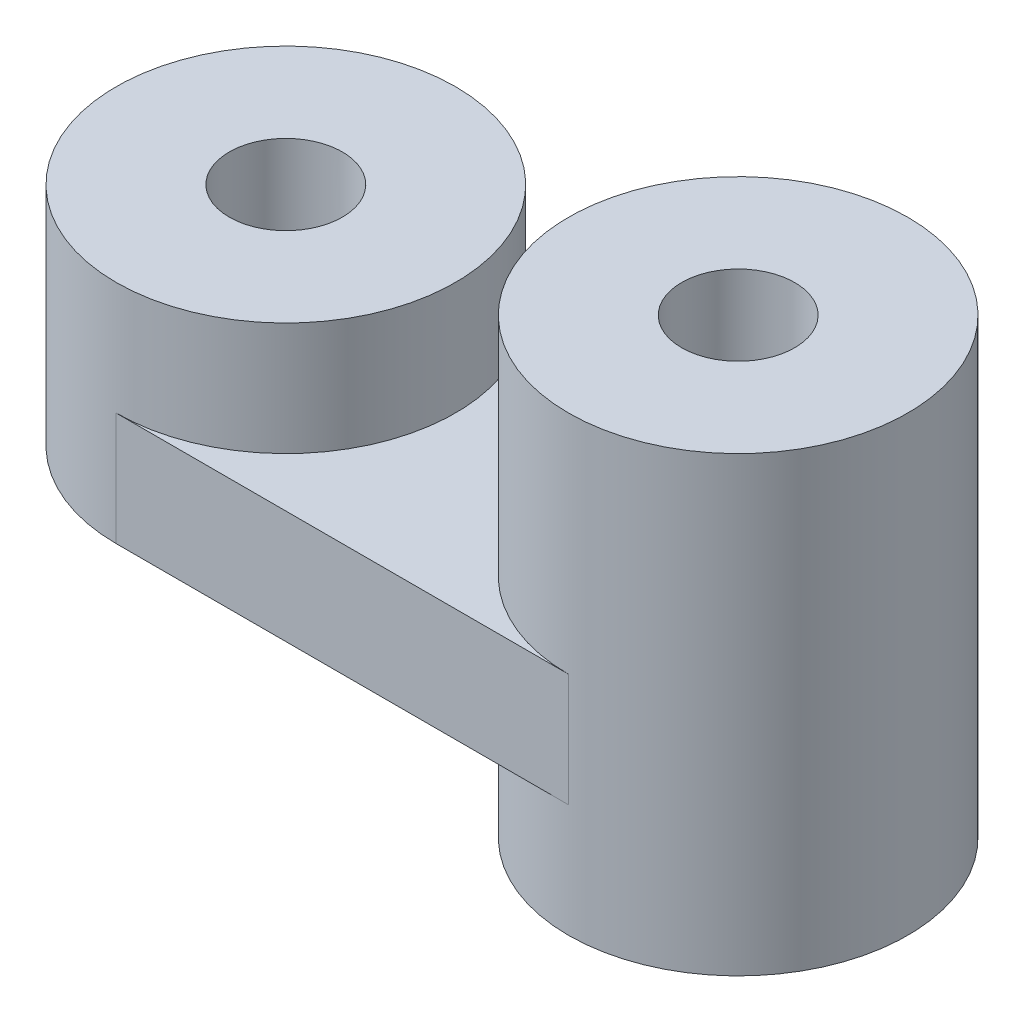
SolidWorks part; units mm, degrees
ref_plane "Alzado" through (0, 0, 0) normal (0, 0, 1) x (1, 0, 0)
ref_plane "Planta" through (0, 0, 0) normal (0, 1, 0) x (1, 0, 0)
ref_plane "Vista lateral" through (0, 0, 0) normal (1, 0, 0) x (0, 0, -1)
sketch "Croquis1" plane through (0, 0, 0) normal (0, 1, 0) x (1, 0, 0)
  line L0 (0, 0) -> (-5, 0) construction
  line L5 (0, 0) -> (15, 0)
  line L6 (0, 0) -> (0, -15)
  line L7 (0, -15) -> (15, -15)
  line L8 (15, 0) -> (15, -15)
  line L9 (0, 0) -> (-20, 0)
  line L10 (0, 0) -> (0, -15)
  line L11 (0, -15) -> (-20, -15)
  line L12 (-20, 0) -> (-20, -15)
  line L13 (-5, 0) -> (-5, -15)
  circle A0 centre (7.5, -7.5) radius 7.5
  circle A1 centre (-12.5, -7.5) radius 7.5
  dimension "D1" = 15
  dimension "D2" = 15
  dimension "D3" = 20
  dimension "D4" = 5
extrude "Saliente-Extruir1" add sketch "Croquis1" along normal blind 20 contours A1 | A0 L5
ref_plane "Plano1" through (0, 0, 15) normal (0, 0, 1) x (1, 0, 0)
sketch "Croquis2" plane through (0, 0, 15) normal (0, 0, 1) x (1, 0, 0)
  line L0 (0, 0) -> (-5, 0) construction
  line L1 (-5, 0) -> (-20, 0)
  line L2 (-20, 0) -> (-20, 5)
  line L3 (-20, 20) -> (-20, 0) construction
  line L4 (-20, 5) -> (-5, 5)
  line L5 (-5, 0) -> (-5, 20) construction
  line L6 (-5, 5) -> (-5, 0)
  dimension "D1" = 5
extrude "Cortar-Extruir1" cut sketch "Croquis2" against normal blind 20
sketch "Croquis3" plane through (0, 0, 15) normal (0, 0, 1) x (1, 0, 0)
  line L0 (-5, 20) -> (-20, 20)
  line L1 (-20, 20) -> (-20, 15)
  line L2 (-20, 20) -> (-20, 5) construction
  line L3 (-20, 15) -> (-5, 15)
  line L4 (-5, 5) -> (-5, 20) construction
  line L5 (-5, 15) -> (-5, 20)
  dimension "D1" = 5
extrude "Cortar-Extruir2" cut sketch "Croquis3" against normal blind 20
sketch "Croquis4" plane through (0, 15, 0) normal (0, 1, 0) x (1, 0, 0)
  line L0 (-12.5, 0) -> (-12.5, -15) construction
  line L1 (-11, -15) -> (11, -15) construction
  circle A0 centre (-12.5, -7.5) radius 7.5 construction
  circle A2 centre (-12.5, -7.5) radius 2.5
  dimension "D1" = 5
extrude "Cortar-Extruir3" cut sketch "Croquis4" against normal blind 20
sketch "Croquis5" plane through (0, 20, 0) normal (0, 1, 0) x (1, 0, 0)
  circle A1 centre (7.5, -7.5) radius 2.5
  dimension "D1" = 5
extrude "Cortar-Extruir4" cut sketch "Croquis5" against normal blind 20
sketch "Croquis6" plane through (0, 0, 15) normal (0, 0, 1) x (1, 0, 0)
  line L0 (-20, 5) -> (-12.5, 5) construction
  line L2 (-20, 5) -> (-5, 5) construction
  line L3 (15, 5) -> (7.5, 5) construction
  line L4 (15, 0) -> (15, 20) construction
  line L5 (-12.5, 5) -> (7.5, 5)
  line L7 (7.5, 10) -> (-12.5, 10)
  dimension "D1" = 7.5
  dimension "D2" = 7.5
  dimension "D3" = 5
extrude "Extruir-Lámina1" add sketch "Croquis6" against normal blind 15 thin thin type one direction reverse wall 2.5
